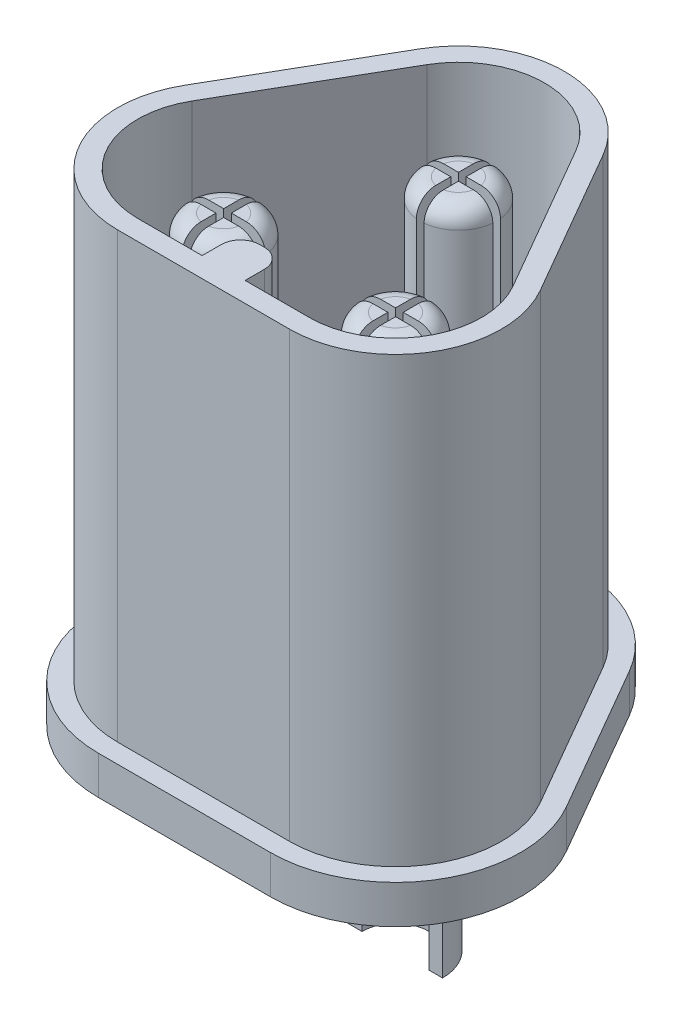
SolidWorks part; units mm, degrees
ref_plane "Front Plane" through (0, 0, 0) normal (0, 0, 1) x (1, 0, 0)
ref_plane "Top Plane" through (0, 0, 0) normal (0, 1, 0) x (1, 0, 0)
ref_plane "Right Plane" through (0, 0, 0) normal (1, 0, 0) x (0, 0, -1)
sketch "Sketch1" plane through (0, 0, 0) normal (0, 1, 0) x (1, 0, 0)
  line L0 (0, 3.3412) -> (0, -2.5882) construction
  line L1 (-1.4588, 0) -> (2.2588, 0) construction
  line L2 (-4.6301, 1.3804) -> (-2.3909, 5.2588)
  line L3 (2.3909, 5.2588) -> (4.6301, 1.3804)
  line L4 (-2.2392, -2.7608) -> (2.2392, -2.7608)
  line L5 (-2.2392, 0) -> (2.2392, 0) construction
  line L6 (0, 3.8785) -> (2.2392, 0) construction
  line L7 (2.2408, 3.8785) -> (2.7608, 3.8785) construction
  line L8 (-4.1798, 1.1204) -> (-1.9406, 4.9988)
  line L9 (4.1798, 1.1204) -> (1.9406, 4.9988)
  line L10 (-2.2392, -2.2408) -> (2.2392, -2.2408)
  line L12 (-0.56, -1.2408) -> (0.56, -1.2408)
  line L13 (-0.56, -1.2408) -> (-0.56, -2.2408)
  line L14 (-0.56, -2.2408) -> (0.56, -2.2408)
  line L15 (0.56, -1.2408) -> (0.56, -2.2408)
  line L16 (-0.56, -1.2408) -> (0.56, -2.2408) construction
  line L17 (-0.56, -2.2408) -> (0.56, -1.2408) construction
  circle A0 centre (-2.2392, 0) radius 2.7608
  circle A1 centre (2.2392, 0) radius 2.7608
  circle A2 centre (0, 3.8785) radius 2.7608
  circle A3 centre (0, 3.8785) radius 2.2408
  circle A4 centre (-2.2392, 0) radius 2.2408
  circle A5 centre (2.2392, 0) radius 2.2408
  point P11 (5, 0)
  point P12 (-5, 0)
  point P13 (0, 6.6392)
  point P29 (0, -1.7408)
  dimension "D1" = 10
  dimension "D2" = 9.4
  dimension "D3" = 0.52
  dimension "D4" = 1.12
  dimension "D5" = 1
extrude "Boss-Extrude1" add sketch "Sketch1" along normal blind 7.5 contours A4 L8 A0 L10 | A1 L10 A0 L4 | A5 L10 A1 L9 | A2 L9 A1 L3 | A3 L9 A2 L8 | A2 L2 A0 L8 | L15 L14 L13 L12
fillet "Fillet1" radius 0.5 2 edges at (-0.56, 3.75, 1.2408) (0.56, 3.75, 1.2408)
sketch "Sketch2" plane through (0, 0, 0) normal (0, -1, 0) x (1, 0, 0)
  line L3 (2.2392, 2.7608) -> (-2.2392, 2.7608)
  line L4 (-4.6301, -1.3804) -> (-2.3909, -5.2588)
  line L5 (2.3909, -5.2588) -> (4.6301, -1.3804)
  line L6 (2.2392, 2.7608) -> (-2.2392, 2.7608)
  line L7 (-4.6301, -1.3804) -> (-2.3909, -5.2588)
  line L8 (2.3909, -5.2588) -> (4.6301, -1.3804)
  arc A3 (4.6301, -1.3804) -> (2.2392, 2.7608) centre (2.2392, 0) ccw
  arc A4 (-2.2392, 2.7608) -> (-4.6301, -1.3804) centre (-2.2392, 0) ccw
  arc A5 (-2.3909, -5.2588) -> (2.3909, -5.2588) centre (0, -3.8785) ccw
  arc A6 (4.6301, -1.3804) -> (2.2392, 2.7608) centre (2.2392, 0) ccw
  arc A7 (-2.2392, 2.7608) -> (-4.6301, -1.3804) centre (-2.2392, 0) ccw
  arc A8 (-2.3909, -5.2588) -> (2.3909, -5.2588) centre (0, -3.8785) ccw
  dimension "D1" = 0
extrude "Boss-Extrude2" add sketch "Sketch2" along normal blind 1.5
sketch "Sketch3" plane through (0, -1.5, 0) normal (0, -1, 0) x (1, 0, 0)
  line L0 (-2.2392, 2.2408) -> (-0.56, 2.2408) construction
  line L1 (-4.1798, -1.1204) -> (-1.9406, -4.9988) construction
  line L2 (0.56, 2.2408) -> (2.2392, 2.2408) construction
  line L3 (2.2392, 2.7608) -> (-2.2392, 2.7608)
  line L4 (-4.6301, -1.3804) -> (-2.3909, -5.2588)
  line L5 (2.3909, -5.2588) -> (4.6301, -1.3804)
  line L6 (2.2392, 2.7608) -> (-2.2392, 2.7608)
  line L7 (-4.6301, -1.3804) -> (-2.3909, -5.2588)
  line L8 (2.3909, -5.2588) -> (4.6301, -1.3804)
  line L9 (4.1798, -1.1204) -> (1.9406, -4.9988) construction
  line L10 (-2.2392, 2.2408) -> (-0.56, 2.2408)
  line L11 (-4.1798, -1.1204) -> (-1.9406, -4.9988)
  line L12 (0.56, 2.2408) -> (2.2392, 2.2408)
  line L13 (4.1798, -1.1204) -> (1.9406, -4.9988)
  line L14 (0.56, 2.2408) -> (-0.56, 2.2408)
  arc A0 (-2.2392, 2.2408) -> (-4.1798, -1.1204) centre (-2.2392, 0) ccw construction
  arc A1 (-1.9406, -4.9988) -> (1.9406, -4.9988) centre (0, -3.8785) ccw construction
  arc A2 (4.1798, -1.1204) -> (2.2392, 2.2408) centre (2.2392, 0) ccw construction
  arc A3 (4.6301, -1.3804) -> (2.2392, 2.7608) centre (2.2392, 0) ccw
  arc A4 (-2.2392, 2.7608) -> (-4.6301, -1.3804) centre (-2.2392, 0) ccw
  arc A5 (-2.3909, -5.2588) -> (2.3909, -5.2588) centre (0, -3.8785) ccw
  arc A6 (4.6301, -1.3804) -> (2.2392, 2.7608) centre (2.2392, 0) ccw
  arc A7 (-2.2392, 2.7608) -> (-4.6301, -1.3804) centre (-2.2392, 0) ccw
  arc A8 (-2.3909, -5.2588) -> (2.3909, -5.2588) centre (0, -3.8785) ccw
  arc A9 (-2.2392, 2.2408) -> (-4.1798, -1.1204) centre (-2.2392, 0) ccw
  arc A10 (-1.9406, -4.9988) -> (1.9406, -4.9988) centre (0, -3.8785) ccw
  arc A11 (4.1798, -1.1204) -> (2.2392, 2.2408) centre (2.2392, 0) ccw
  dimension "D1" = 0
extrude "Boss-Extrude3" add sketch "Sketch3" along normal offset from surface (3.56 mm away) 12.56 up to face at (0, 7.5, 0.2067)
sketch "Sketch4" plane through (0, -5.06, 0) normal (0, -1, 0) x (1, 0, 0)
  line L0 (4.6301, -1.3804) -> (2.3909, -5.2588) construction
  line L1 (-2.3909, -5.2588) -> (-4.6301, -1.3804) construction
  line L2 (-2.2392, 2.7608) -> (2.2392, 2.7608) construction
  line L3 (4.6301, -1.3804) -> (2.3909, -5.2588)
  line L4 (-2.3909, -5.2588) -> (-4.6301, -1.3804)
  line L5 (-2.2392, 2.7608) -> (2.2392, 2.7608)
  line L6 (-2.2392, 3.2608) -> (2.2392, 3.2608)
  line L7 (5.0631, -1.6304) -> (2.8239, -5.5088)
  line L8 (-2.8239, -5.5088) -> (-5.0631, -1.6304)
  arc A0 (4.6301, -1.3804) -> (2.2392, 2.7608) centre (2.2392, 0) ccw construction
  arc A1 (-2.3909, -5.2588) -> (2.3909, -5.2588) centre (0, -3.8785) ccw construction
  arc A2 (-2.2392, 2.7608) -> (-4.6301, -1.3804) centre (-2.2392, 0) ccw construction
  arc A3 (4.6301, -1.3804) -> (2.2392, 2.7608) centre (2.2392, 0) ccw
  arc A4 (-2.3909, -5.2588) -> (2.3909, -5.2588) centre (0, -3.8785) ccw
  arc A5 (-2.2392, 2.7608) -> (-4.6301, -1.3804) centre (-2.2392, 0) ccw
  arc A6 (5.0631, -1.6304) -> (2.2392, 3.2608) centre (2.2392, 0) ccw
  arc A7 (-2.8239, -5.5088) -> (2.8239, -5.5088) centre (0, -3.8785) ccw
  arc A8 (-2.2392, 3.2608) -> (-5.0631, -1.6304) centre (-2.2392, 0) ccw
  dimension "D1" = 0.5
extrude "Boss-Extrude4" add sketch "Sketch4" against normal blind 1
sketch "Sketch5" plane through (0, -1.5, 0) normal (0, -1, 0) x (1, 0, 0)
  circle A0 centre (-2.2392, 0) radius 1.225
  circle A1 centre (2.2392, 0) radius 1.225
  circle A2 centre (0, -3.8785) radius 1.225
  circle A3 centre (-2.2392, 0) radius 0.875
  circle A4 centre (2.2392, 0) radius 0.875
  circle A5 centre (0, -3.8785) radius 0.875
  dimension "D1" = 2.45
  dimension "D2" = 0.35
extrude "Boss-Extrude5" add sketch "Sketch5" along normal offset from surface (6.41 mm away) 2.85 up to face at (0, -5.06, -1.2928) offset beyond the face yes
sketch "Sketch6" plane through (0, -7.91, 0) normal (0, -1, 0) x (1, 0, 0)
  line L0 (-3.4642, 0) -> (-1.0142, 0)
  line L1 (1.0142, 0) -> (3.4642, 0)
  line L2 (-1.225, -3.8785) -> (1.225, -3.8785)
  circle A0 centre (0, -3.8785) radius 1.225 construction
  circle A1 centre (2.2392, 0) radius 1.225 construction
  circle A2 centre (-2.2392, 0) radius 1.225 construction
  circle A3 centre (0, -3.8785) radius 1.225
  circle A4 centre (2.2392, 0) radius 1.225
  circle A5 centre (-2.2392, 0) radius 1.225
  circle M3 centre (-2.2392, 0) radius 0.875
  circle M4 centre (-2.2392, 0) radius 1.225
extrude "Cut-Extrude1" cut sketch "Sketch6" against normal blind 2.65 contours L0 M4 M3 | L1 A4 | L2 A3
sketch "Sketch7" plane through (0, 0, 0) normal (0, 1, 0) x (1, 0, 0)
  circle A0 centre (-2.2392, 0) radius 1.225 construction
  circle A1 centre (2.2392, 0) radius 1.225 construction
  circle A2 centre (0, 3.8785) radius 1.225 construction
  circle A3 centre (-2.2392, 0) radius 1.225
  circle A4 centre (2.2392, 0) radius 1.225
  circle A5 centre (0, 3.8785) radius 1.225
extrude "Boss-Extrude6" add sketch "Sketch7" along normal blind 0.25
sketch "Sketch8" plane through (0, 0.25, 0) normal (0, 1, 0) x (1, 0, 0)
  circle A0 centre (0, 3.8785) radius 1
  circle A1 centre (-2.2392, 0) radius 1
  circle A2 centre (2.2392, 0) radius 1
  dimension "D1" = 2
extrude "Boss-Extrude7" add sketch "Sketch8" along normal offset from surface (6.25 mm away) 1 up to face at (0, 7.5, 0.2067)
fillet "Fillet2" radius 0.5 3 edges at (2.2392, 6.5, 1) (-2.2392, 6.5, 1) (0, 6.5, -2.8785)
sketch "Sketch9" plane through (0, 6.5, 0) normal (0, 1, 0) x (1, 0, 0)
  line L0 (0, 0) -> (0, -1.2408) construction
  line L1 (-0.1, 4.8785) -> (0.1, 4.8785)
  line L2 (-0.1, 4.8785) -> (-0.1, 2.8785)
  line L3 (-0.1, 2.8785) -> (0.1, 2.8785)
  line L4 (0.1, 4.8785) -> (0.1, 2.8785)
  line L5 (-0.1, 4.8785) -> (0.1, 2.8785) construction
  line L6 (-0.1, 2.8785) -> (0.1, 4.8785) construction
  line L7 (-1, 3.9785) -> (1, 3.9785)
  line L8 (-1, 3.9785) -> (-1, 3.7785)
  line L9 (-1, 3.7785) -> (1, 3.7785)
  line L10 (1, 3.9785) -> (1, 3.7785)
  line L11 (-1, 3.9785) -> (1, 3.7785) construction
  line L12 (-1, 3.7785) -> (1, 3.9785) construction
  line L13 (-2.3392, 1) -> (-2.1392, 1)
  line L14 (-2.3392, 1) -> (-2.3392, -1)
  line L15 (-2.3392, -1) -> (-2.1392, -1)
  line L16 (-2.1392, 1) -> (-2.1392, -1)
  line L17 (-2.3392, 1) -> (-2.1392, -1) construction
  line L18 (-2.3392, -1) -> (-2.1392, 1) construction
  line L19 (-3.2392, 0.1) -> (-1.2392, 0.1)
  line L20 (-3.2392, 0.1) -> (-3.2392, -0.1)
  line L21 (-3.2392, -0.1) -> (-1.2392, -0.1)
  line L22 (-1.2392, 0.1) -> (-1.2392, -0.1)
  line L23 (-3.2392, 0.1) -> (-1.2392, -0.1) construction
  line L24 (-3.2392, -0.1) -> (-1.2392, 0.1) construction
  line L25 (-0.06, -1.2408) -> (0.06, -1.2408) construction
  line L26 (2.3392, 1) -> (2.1392, 1)
  line L27 (2.3392, 1) -> (2.3392, -1)
  line L28 (2.3392, -1) -> (2.1392, -1)
  line L29 (2.1392, 1) -> (2.1392, -1)
  line L30 (3.2392, 0.1) -> (3.2392, -0.1)
  line L31 (3.2392, 0.1) -> (1.2392, 0.1)
  line L32 (1.2392, 0.1) -> (1.2392, -0.1)
  line L33 (3.2392, -0.1) -> (1.2392, -0.1)
  circle A0 centre (0, 3.8785) radius 1 construction
  circle A1 centre (-2.2392, 0) radius 1 construction
  point P0 (0, 3.8785)
  point P8 (0, 3.8785)
  point P13 (-2.2392, 0)
  point P21 (-2.2392, 0)
  dimension "D1" = 0.2
extrude "Cut-Extrude2" cut sketch "Sketch9" against normal blind 5 contours L21 L22 L19 L20 | L16 L15 L14 L13 | L33 L32 L31 L30 | L29 L28 L27 L26 | L9 L10 L7 L8 | L4 L3 L2 L1
